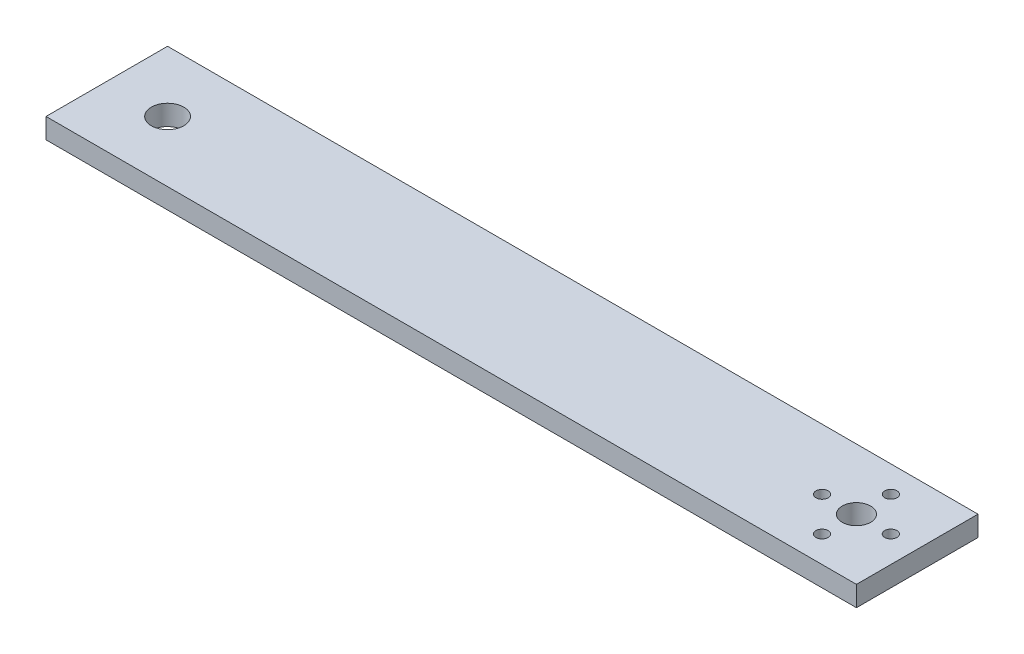
SolidWorks part; units mm, degrees
ref_plane "Front Plane" through (0, 0, 0) normal (0, 0, 1) x (1, 0, 0)
ref_plane "Top Plane" through (0, 0, 0) normal (0, 1, 0) x (1, 0, 0)
ref_plane "Right Plane" through (0, 0, 0) normal (1, 0, 0) x (0, 0, -1)
sketch "Sketch1" plane through (0, 0, 0) normal (0, 1, 0) x (1, 0, 0)
  line L1 (0, 0) -> (200, 0)
  line L2 (0, 0) -> (0, 30)
  line L3 (0, 30) -> (200, 30)
  line L4 (200, 0) -> (200, 30)
  dimension "D1" = 30
  dimension "D2" = 200
extrude "Boss-Extrude1" add sketch "Sketch1" along normal blind 5
sketch "Sketch2" plane through (0, 5, 0) normal (0, 1, 0) x (1, 0, 0)
  circle A0 centre (15, 15) radius 4
  circle A1 centre (185, 15) radius 3.5
  circle A3 centre (185, 23.5) radius 1.5
  circle A4 centre (193.4791, 15) radius 1.5
  circle A5 centre (176.5209, 15) radius 1.5
  circle A6 centre (185, 6.5) radius 1.5
extrude "Cut-Extrude1" cut sketch "Sketch2" against normal blind 5
